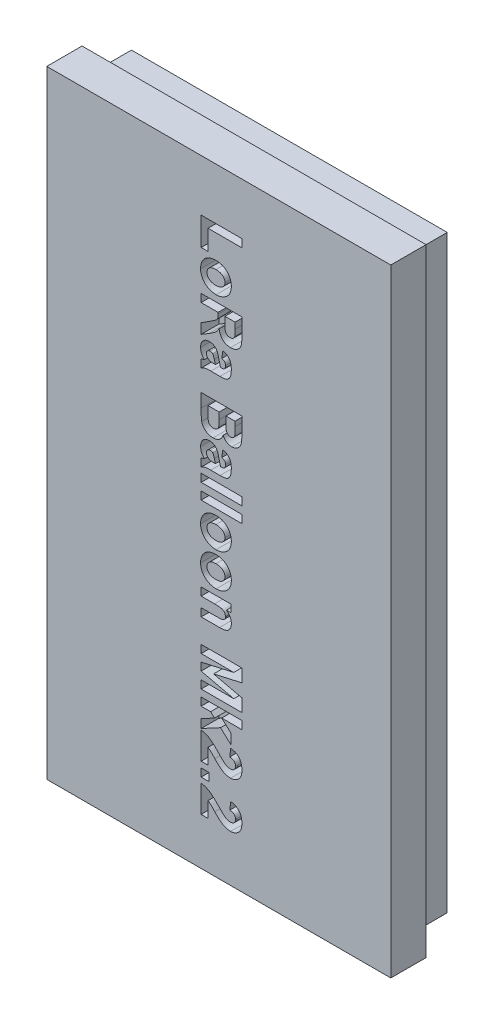
SolidWorks part; units mm, degrees
ref_plane "Front Plane" through (0, 0, 0) normal (0, 0, 1) x (1, 0, 0)
ref_plane "Top Plane" through (0, 0, 0) normal (0, 1, 0) x (1, 0, 0)
ref_plane "Right Plane" through (0, 0, 0) normal (1, 0, 0) x (0, 0, -1)
sketch "Sketch1" plane through (0, 0, 0) normal (0, 0, 1) x (1, 0, 0)
  line L1 (0, 0) -> (39, 0)
  line L2 (0, 0) -> (0, 70)
  line L3 (0, 70) -> (39, 70)
  line L4 (39, 0) -> (39, 70)
  dimension "D1" = 70
  dimension "D2" = 39
extrude "Base" add sketch "Sketch1" along normal blind 4
sketch "Sketch2" plane through (0, 0, 0) normal (0, 0, -1) x (-1, 0, 0)
  line L0 (-39, 0) -> (-39, 70) construction
  line L1 (-37.4, 68.4) -> (-35.6, 68.4)
  line L2 (-37.4, 68.4) -> (-37.4, 1.6)
  line L3 (-37.4, 1.6) -> (-35.6, 1.6)
  line L4 (-35.6, 68.4) -> (-35.6, 1.6)
  line L5 (0, 0) -> (-39, 0) construction
  line L6 (0, 70) -> (0, 0) construction
  line L7 (-35.6, 1.6) -> (-1.6, 1.6)
  line L8 (-35.6, 1.6) -> (-35.6, 3.4)
  line L9 (-35.6, 3.4) -> (-1.6, 3.4)
  line L10 (-1.6, 1.6) -> (-1.6, 3.4)
  line L12 (-39, 70) -> (0, 70) construction
  line L13 (-39, 35) -> (0, 35) construction
  line L14 (-19.5, 70) -> (-19.5, 0) construction
  line L15 (-35.6, 66.6) -> (-1.6, 66.6)
  line L16 (-1.6, 68.4) -> (-1.6, 66.6)
  line L17 (-35.6, 68.4) -> (-1.6, 68.4)
  line L18 (-35.6, 68.4) -> (-35.6, 66.6)
  line L19 (-1.6, 1.6) -> (-3.4, 1.6)
  line L20 (-3.4, 68.4) -> (-3.4, 1.6)
  line L21 (-1.6, 68.4) -> (-3.4, 68.4)
  line L22 (-1.6, 68.4) -> (-1.6, 1.6)
  dimension "D1" = 1.6
  dimension "D2" = 1.8
  dimension "D3" = 1.6
  dimension "D4" = 1.8
extrude "Mount" add sketch "Sketch2" along normal blind 4 contours L4 L1 L2 L3 | L22 L15 L20 L9 | L20 L9 L4 L7 | L9 L20 L7 L10 | L17 L20 L15 L16 | L20 L17 L4 L15
sketch "Sketch3" plane through (0, 0, 4) normal (0, 0, 1) x (1, 0, 0)
  line L0 (17.5, 0) -> (17.5, 70) construction
  line L1 (19.5, 0) -> (19.5, 5) construction
  line L2 (19.5, 70) -> (19.5, 65) construction
  line L3 (39, 70) -> (0, 70) construction
  line L4 (0, 0) -> (39, 0) construction
  line L6 (0, 70) -> (0, 0) construction
  text T0 "<b>  LoRa Balloon Mk2.2</b>" font "Arial Narrow" height in points 18
  dimension "D1" = 17.5
  dimension "D2" = 70
  dimension "D3" = 5
  dimension "D4" = 5
extrude "Name" cut sketch "Sketch3" against normal blind 2
